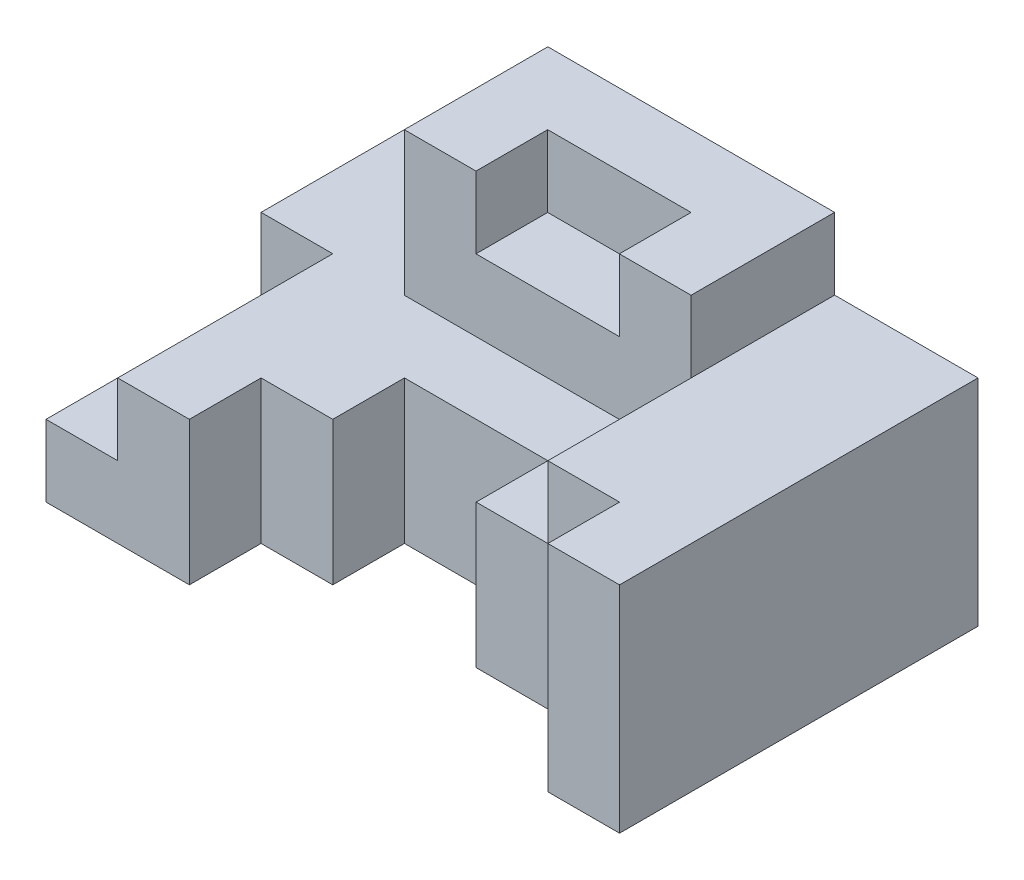
SolidWorks part; units mm, degrees
ref_plane "Front Plane" through (0, 0, 0) normal (0, 0, 1) x (1, 0, 0)
ref_plane "Top Plane" through (0, 0, 0) normal (0, 1, 0) x (1, 0, 0)
ref_plane "Right Plane" through (0, 0, 0) normal (1, 0, 0) x (0, 0, -1)
sketch "Sketch1" plane through (0, 0, 0) normal (0, 1, 0) x (1, 0, 0)
  line L1 (-40, -25) -> (40, -25)
  line L2 (-40, -25) -> (-40, 25)
  line L3 (-40, 25) -> (40, 25)
  line L4 (40, -25) -> (40, 25)
  line L5 (-40, -25) -> (40, 25) construction
  line L6 (-40, 25) -> (40, -25) construction
  point P0 (0, 0)
  dimension "D1" = 50
  dimension "D2" = 80
extrude "Boss-Extrude1" add sketch "Sketch1" along normal blind 20
sketch "Sketch2" plane through (0, 20, 0) normal (0, 1, 0) x (1, 0, 0)
  line L0 (-20, -25) -> (-20, -15)
  line L1 (-40, -25) -> (40, -25) construction
  line L2 (-20, -15) -> (-10, -15)
  line L3 (-10, -15) -> (-10, -5)
  line L4 (-10, -5) -> (10, -5)
  line L5 (10, -5) -> (10, -15)
  line L6 (10, -15) -> (30, -15)
  line L7 (30, -15) -> (30, -25)
  line L8 (30, -25) -> (-20, -25)
  line L9 (-40, 25) -> (-40, -25) construction
  dimension "D1" = 10
  dimension "D2" = 20
  dimension "D3" = 10
  dimension "D4" = 10
  dimension "D5" = 20
  dimension "D6" = 10
  dimension "D7" = 20
extrude "Cut-Extrude1" cut sketch "Sketch2" against normal blind 20
sketch "Sketch3" plane through (0, 20, 0) normal (0, 1, 0) x (1, 0, 0)
  line L1 (-40, -25) -> (-30, -25)
  line L2 (-40, -25) -> (-40, 5)
  line L3 (-40, 5) -> (-30, 5)
  line L4 (-30, -25) -> (-30, 5)
  dimension "D1" = 10
  dimension "D2" = 30
extrude "Cut-Extrude2" cut sketch "Sketch3" against normal blind 10
sketch "Sketch4" plane through (0, 20, 0) normal (0, 1, 0) x (1, 0, 0)
  line L0 (40, -25) -> (40, 25)
  line L1 (40, 25) -> (20, 25)
  line L2 (40, 25) -> (-40, 25) construction
  line L3 (20, 25) -> (20, -15)
  line L4 (30, -15) -> (10, -15) construction
  line L5 (20, -15) -> (30, -15)
  line L6 (30, -15) -> (30, -25)
  line L7 (30, -25) -> (40, -25)
  dimension "D1" = 10
extrude "Boss-Extrude2" add sketch "Sketch4" along normal blind 10
sketch "Sketch6" plane through (0, 20, 0) normal (0, 1, 0) x (1, 0, 0)
  line L1 (20, 25) -> (-20, 25)
  line L2 (20, 25) -> (20, 4.9773)
  line L3 (20, 4.9773) -> (-20, 4.9773)
  line L4 (-20, 25) -> (-20, 4.9773)
  dimension "D1" = 20.0227
  dimension "D2" = 40
extrude "Boss-Extrude3" add sketch "Sketch6" along normal blind 20
sketch "Sketch7" plane through (0, 40, 0) normal (0, 1, 0) x (1, 0, 0)
  line L0 (-20, 4.9773) -> (20, 4.9773) construction
  line L1 (-10, 4.9773) -> (10, 4.9773)
  line L2 (-10, 4.9773) -> (-10, 14.9773)
  line L3 (-10, 14.9773) -> (10, 14.9773)
  line L4 (10, 4.9773) -> (10, 14.9773)
  line L5 (20, 4.9773) -> (20, 25) construction
  dimension "D1" = 10
  dimension "D2" = 20
  dimension "D3" = 10
extrude "Cut-Extrude3" cut sketch "Sketch7" against normal blind 10
